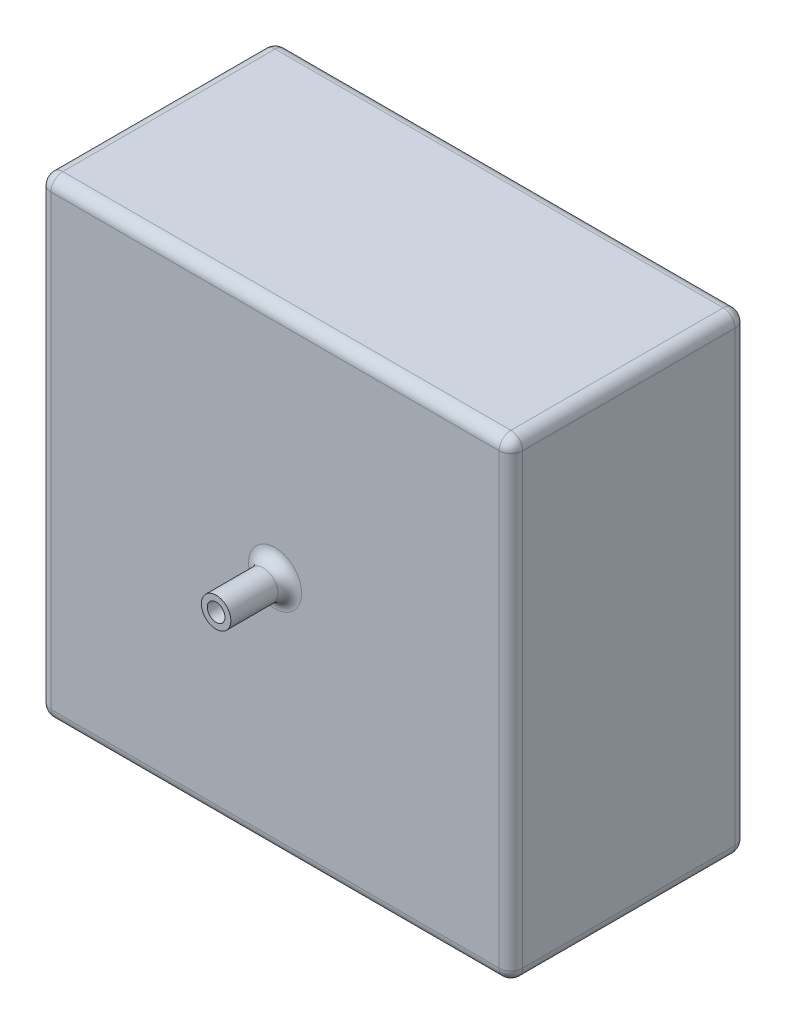
SolidWorks part; units mm, degrees
ref_plane "정면" through (0, 0, 0) normal (0, 0, 1) x (1, 0, 0)
ref_plane "윗면" through (0, 0, 0) normal (0, 1, 0) x (1, 0, 0)
ref_plane "우측면" through (0, 0, 0) normal (1, 0, 0) x (0, 0, -1)
sketch "스케치1" plane through (0, 0, 0) normal (0, 0, 1) x (1, 0, 0)
  line L1 (0, 0) -> (400, 0)
  line L2 (0, 0) -> (0, -400)
  line L3 (0, -400) -> (400, -400)
  line L4 (400, 0) -> (400, -400)
  dimension "D1" = 400
  dimension "D2" = 400
extrude "보스-돌출1" add sketch "스케치1" along normal blind 200
sketch "스케치2" plane through (0, 0, 200) normal (0, 0, 1) x (1, 0, 0)
  line L0 (0, 0) -> (0, -400) construction
  line L1 (0, -400) -> (400, -400) construction
  circle A0 centre (200, -198.5668) radius 12.5
  point P2 (0, 0)
  dimension "D1" = 25
  dimension "D2" = 200
  dimension "D3" = 201.4332
extrude "보스-돌출2" add sketch "스케치2" along normal blind 50
fillet "필렛1" radius 10 13 edges at (400, 0, 100) (400, -200, 0) (200, 0, 0) (0, 0, 100) (0, -200, 0) (200, 0, 200) (400, -200, 200) (0, -200, 200) (212.5, -198.5668, 200) (0, -400, 100) (200, -400, 200) (400, -400, 100) (200, -400, 0)
shell "쉘1" thickness 5
